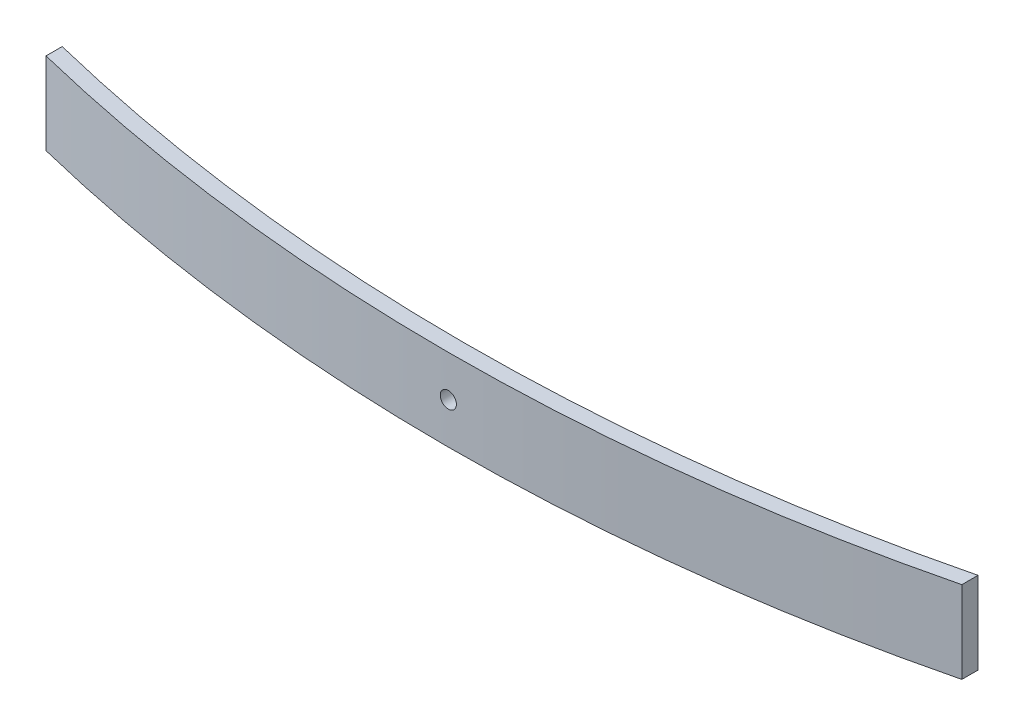
SolidWorks part; units mm, degrees
ref_plane "Front Plane" through (0, 0, 0) normal (0, 0, 1) x (1, 0, 0)
ref_plane "Top Plane" through (0, 0, 0) normal (0, 1, 0) x (1, 0, 0)
ref_plane "Right Plane" through (0, 0, 0) normal (1, 0, 0) x (0, 0, -1)
sketch "Sketch1" plane through (0, 0, 0) normal (0, 1, 0) x (1, 0, 0)
  line L0 (-630, 0) -> (630, 0) construction
  line L1 (-210.8013, -133) -> (245.5549, -133) construction
  line L2 (0, 0) -> (0, -133) construction
  line L3 (-602.5798, 17.4465) -> (-589.9243, 25.4988)
  line L4 (-616.835, -11.5296) -> (-605.5506, -21.4121)
  line L5 (616.835, -11.5296) -> (605.5506, -21.4121)
  line L6 (-630.0217, -47.5) -> (-630.0217, -62.5)
  line L7 (602.5798, 17.4465) -> (589.9243, 25.4988)
  line L8 (630.0217, -47.5) -> (630.0217, -62.5)
  line L9 (-545.0217, -92.3065) -> (-545.0217, -107.3065)
  line L10 (545.0217, -92.3065) -> (545.0217, -107.3065)
  line L11 (-485.0217, -125.4896) -> (-485.0217, -140.4896)
  line L12 (485.0217, -125.4896) -> (485.0217, -140.4896)
  line L13 (-425.0217, -156.3949) -> (-425.0217, -171.3949)
  line L14 (425.0217, -156.3949) -> (425.0217, -171.3949)
  arc A0 (-616.835, -11.5296) -> (-630, -17.5) centre (-630, 0) ccw
  arc A1 (630, -17.5) -> (616.835, -11.5296) centre (630, 0) ccw
  arc A2 (-630, -17.5) -> (630, -17.5) centre (0, 1642.9318) ccw
  arc A3 (-630.0011, -32.5) -> (630.0011, -32.5) centre (0, 1627.9379) ccw
  arc A4 (-605.5506, -21.4121) -> (-630.0011, -32.5) centre (-630, 0) ccw
  arc A5 (630.0011, -32.5) -> (605.5506, -21.4121) centre (630, 0) ccw
  arc A6 (-630.0217, -47.5) -> (630.0217, -47.5) centre (0, 1613.05) ccw
  arc A7 (630.0217, -47.5) -> (589.9243, 25.4988) centre (630, 0) ccw
  arc A8 (-589.9243, 25.4988) -> (-630.0217, -47.5) centre (-630, 0) ccw
  arc A9 (-630.0217, -62.5) -> (630.0217, -62.5) centre (0, 1598.05) ccw
  arc A10 (545.0217, -107.3065) -> (-545.0217, -107.3065) centre (0, 1583.05) cw
  arc A11 (485.0217, -140.4896) -> (-485.0217, -140.4896) centre (0, 1568.05) cw
  arc A12 (425.0217, -171.3949) -> (-425.0217, -171.3949) centre (0, 1553.05) cw
  point P5 (-630.0217, -47.5)
  point P6 (0, -163)
  point P10 (0, -133)
  point P13 (-630.0011, -32.5)
  point P14 (0, -148)
  point P15 (630.0011, -32.5)
  point P20 (630.0217, -47.5)
  point P27 (0, -178)
  point P37 (0, -193)
  point P40 (630.0217, -55)
  point P44 (0, -208)
  point P50 (0, -223)
  dimension "D4" = 35
  dimension "D5" = 35
  dimension "D9" = 15
  dimension "D12" = 15
  dimension "D1" = 133
  dimension "D2" = 630
  dimension "D3" = 630
  dimension "D6" = 15
  dimension "D7" = 15
  dimension "D8" = 15
  dimension "D10" = 15
  dimension "D11" = 15
  dimension "D13" = 15
  dimension "D14" = 15
  dimension "D15" = 15
  dimension "D16" = 85
  dimension "D17" = 15
  dimension "D18" = 15
  dimension "D19" = 85
  dimension "D20" = 60
  dimension "D21" = 15
  dimension "D22" = 15
  dimension "D23" = 15
  dimension "D24" = 60
  dimension "D25" = 15
  dimension "D26" = 60
  dimension "D27" = 15
  dimension "D28" = 60
  dimension "D29" = 15
sketch "Sketch5" plane through (0, 0, 0) normal (0, 0, 1) x (1, 0, 0)
  circle A0 centre (0, 38.1) radius 7.5
  dimension "D2" = 15
  dimension "D1" = 38.1
sketch "Sketch6" plane through (0, 0, 0) normal (0, 0, 1) x (1, 0, 0)
  circle A0 centre (0, 38.1) radius 7.5
sketch "Sketch7" plane through (0, 0, 0) normal (0, 0, 1) x (1, 0, 0)
  circle A0 centre (0, 38.1) radius 7.5
sketch "Sketch8" plane through (0, 0, 0) normal (0, 0, 1) x (1, 0, 0)
  circle A0 centre (0, 38.1) radius 7.5
sketch "Sketch9" plane through (0, 0, 0) normal (0, 0, 1) x (1, 0, 0)
  circle A0 centre (0, 38.1) radius 7.5
extrude "Boss-Extrude1" add sketch "Sketch1" along normal blind 76.2 contours A12 L14 A11 L13
sketch "Sketch10" plane through (0, 0, 0) normal (0, 0, 1) x (1, 0, 0)
  circle A0 centre (0, 38.1) radius 7.5
extrude "Cut-Extrude1" cut sketch "Sketch10" along normal through all
